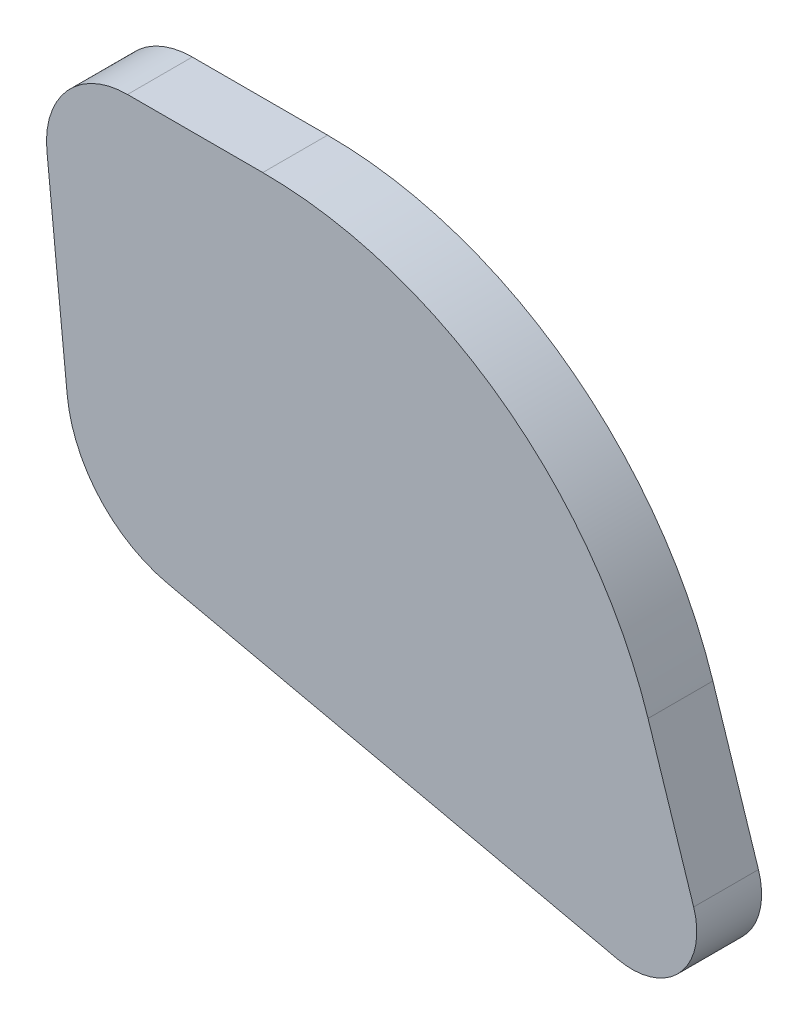
SolidWorks part; units mm, degrees
ref_plane "Front Plane" through (0, 0, 0) normal (0, 0, 1) x (1, 0, 0)
ref_plane "Top Plane" through (0, 0, 0) normal (0, 1, 0) x (1, 0, 0)
ref_plane "Right Plane" through (0, 0, 0) normal (1, 0, 0) x (0, 0, -1)
sketch "Sketch1" plane through (0, 0, 0) normal (0, 0, 1) x (1, 0, 0)
  line L0 (96, 288) -> (480, 288) construction
  line L1 (147.5185, 207.0368) -> (155.868, 207.0368)
  line L2 (179.6486, 189.7494) -> (182.4617, 181.0757)
  line L3 (177.7861, 175.9376) -> (150.0125, 182.1317)
  line L4 (143.7943, 189.137) -> (142.5438, 201.535)
  arc A0 (147.5185, 207.0368) -> (142.5438, 201.535) centre (147.5185, 202.0368) ccw
  arc A1 (155.868, 207.0368) -> (179.6486, 189.7494) centre (155.868, 182.0368) cw
  arc A2 (182.4617, 181.0757) -> (177.7861, 175.9376) centre (178.6568, 179.8417) cw
  arc A3 (150.0125, 182.1317) -> (143.7943, 189.137) centre (151.7539, 189.9399) cw
  dimension "D1" = 5
  dimension "D2" = 25
  dimension "D3" = 4
  dimension "D4" = 8
extrude "Boss-Extrude1" add sketch "Sketch1" along normal blind 4
scale "Scale1" scale about centroid uniform scaling yes scale factor 0.709677
scale "Scale2" scale about centroid uniform scaling yes scale factor 1.107011
